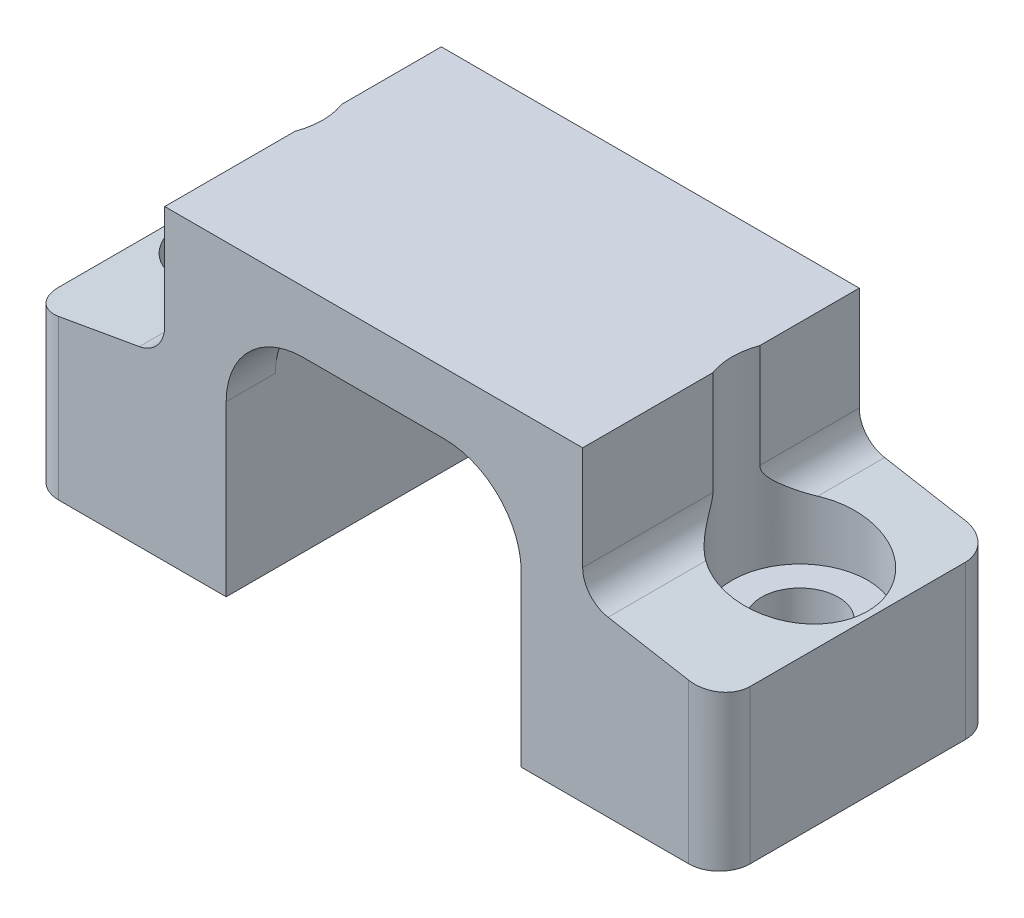
SolidWorks part; units mm, degrees
ref_plane "Front Plane" through (0, 0, 0) normal (0, 0, 1) x (1, 0, 0)
ref_plane "Top Plane" through (0, 0, 0) normal (0, 1, 0) x (1, 0, 0)
ref_plane "Right Plane" through (0, 0, 0) normal (1, 0, 0) x (0, 0, -1)
sketch "Sketch1" plane through (0, 0, 0) normal (0, 0, 1) x (1, 0, 0)
  line L0 (-92.6582, 0) -> (89.2369, 0) construction
  line L2 (-6.096, 10.16) -> (6.096, 10.16)
  line L3 (6.096, 10.16) -> (6.096, 0)
  line L4 (-6.096, 0) -> (6.096, 0) construction
  line L5 (8.89, 6.35) -> (14.2875, 6.35) construction
  line L6 (14.2875, 6.35) -> (14.2875, 0)
  line L7 (14.2875, 0) -> (6.096, 0)
  line L8 (8.636, 7.3465) -> (8.636, 12.7)
  line L9 (8.636, 12.7) -> (-8.636, 12.7)
  line L10 (0, 0) -> (0, 31.7739) construction
  line L13 (-8.636, 7.3465) -> (-8.636, 12.7)
  line L14 (-8.89, 6.35) -> (-14.2875, 6.35) construction
  line L15 (-14.2875, 6.35) -> (-14.2875, 0)
  line L16 (-14.2875, 0) -> (-6.096, 0)
  line L17 (-6.096, 10.16) -> (-6.096, 0)
  line L18 (14.2875, 6.35) -> (8.636, 7.3465)
  line L19 (-14.2875, 6.35) -> (-8.636, 7.3465)
  point P5 (0, 0)
  point P16 (0, 12.7)
  point P24 (0, 10.16)
  dimension "D1" = 10.16
  dimension "D2" = 2.54
  dimension "D3" = 12.192
  dimension "D4" = 12.7
  dimension "D5" = 6.35
  dimension "D7" = 28.575
  dimension "D8" = 10
  dimension "D9" = 10
extrude "Boss-Extrude1" add sketch "Sketch1" against normal blind 22.86
sketch "Sketch2" plane through (0, 0, 0) normal (0, 0, 1) x (1, 0, 0)
  line L0 (6.096, 10.16) -> (6.096, 0) construction
  line L1 (-6.096, 10.16) -> (6.096, 10.16) construction
  line L2 (6.096, 6.985) -> (6.096, 0) construction
  line L3 (-6.096, 10.16) -> (2.921, 10.16) construction
  line L4 (2.921, 10.16) -> (6.096, 10.16)
  line L5 (6.096, 10.16) -> (6.096, 6.985)
  line L6 (0, 0) -> (0, 17.4905) construction
  line L7 (-6.096, 10.16) -> (-6.096, 6.985)
  line L8 (-2.921, 10.16) -> (-6.096, 10.16)
  arc A0 (6.096, 6.985) -> (2.921, 10.16) centre (2.921, 6.985) ccw
  arc A1 (-6.096, 6.985) -> (-2.921, 10.16) centre (-2.921, 6.985) cw
  dimension "D1" = 3.175
extrude "Boss-Extrude2" add sketch "Sketch2" against normal blind 13.462
sketch "Sketch3" plane through (0, 0, -13.462) normal (0, 0, 1) x (1, 0, 0)
  line L2 (-6.096, 10.16) -> (-6.096, 6.985)
  line L3 (-2.921, 10.16) -> (-6.096, 10.16)
  line L4 (-6.096, 10.16) -> (-6.096, 6.985)
  line L5 (-2.921, 10.16) -> (-6.096, 10.16)
  line L6 (6.096, 10.16) -> (2.921, 10.16)
  line L7 (6.096, 6.985) -> (6.096, 10.16)
  line L8 (6.096, 10.16) -> (2.921, 10.16) construction
  line L9 (6.096, 6.985) -> (6.096, 10.16) construction
  arc A1 (-2.921, 10.16) -> (-6.096, 6.985) centre (-2.921, 6.985) ccw
  arc A2 (-2.921, 10.16) -> (-6.096, 6.985) centre (-2.921, 6.985) ccw
  arc A3 (6.096, 6.985) -> (2.921, 10.16) centre (2.921, 6.985) ccw
  arc A4 (6.096, 6.985) -> (2.921, 10.16) centre (2.921, 6.985) ccw construction
  dimension "D1" = 0
  dimension "D2" = 0
extrude "Boss-Extrude3" add sketch "Sketch3" against normal blind 1.905 from offset 1.27 offset against normal yes
sketch "Sketch4" plane through (0, 0, -16.637) normal (0, 0, 1) x (1, 0, 0)
  line L2 (-6.096, 10.16) -> (-6.096, 6.985)
  line L3 (-2.921, 10.16) -> (-6.096, 10.16)
  line L4 (-6.096, 10.16) -> (-6.096, 6.985)
  line L5 (-2.921, 10.16) -> (-6.096, 10.16)
  arc A1 (-2.921, 10.16) -> (-6.096, 6.985) centre (-2.921, 6.985) ccw
  arc A2 (-2.921, 10.16) -> (-6.096, 6.985) centre (-2.921, 6.985) ccw
  dimension "D1" = 0
extrude "Boss-Extrude4" add sketch "Sketch4" against normal blind 3.81 from offset 1.27 offset against normal yes
sketch "Sketch5" plane through (0, 0, 0) normal (0, 1, 0) x (1, 0, 0)
  line L0 (-5.9055, 22.0472) -> (5.9055, 22.0472)
  line L1 (5.9055, 22.0472) -> (5.9055, 22.86)
  line L2 (5.9055, 22.86) -> (-5.9055, 22.86)
  line L3 (-5.9055, 22.86) -> (-5.9055, 22.0472)
  line L5 (-5.9055, 17.018) -> (5.9055, 17.018)
  line L6 (-5.9055, 17.018) -> (-5.9055, 17.8308)
  line L7 (-5.9055, 17.8308) -> (5.9055, 17.8308)
  line L8 (5.9055, 17.018) -> (5.9055, 17.8308)
  line L9 (-5.9055, 13.8176) -> (5.9055, 13.8176)
  line L10 (-5.9055, 13.8176) -> (-5.9055, 14.6304)
  line L11 (-5.9055, 14.6304) -> (5.9055, 14.6304)
  line L12 (5.9055, 13.8176) -> (5.9055, 14.6304)
  line L13 (-5.9055, 13.8176) -> (5.9055, 13.8176)
  line L14 (-5.9055, 13.8176) -> (-5.9055, -1.27)
  line L15 (-5.9055, -1.27) -> (5.9055, -1.27)
  line L16 (5.9055, 13.8176) -> (5.9055, -1.27)
  line L17 (-6.096, 22.86) -> (6.096, 22.86) construction
  point P12 (0, 22.0472)
  dimension "D1" = 0.8128
  dimension "D2" = 11.811
  dimension "D3" = 5.842
  dimension "D4" = 4.0132
  dimension "D5" = 24.13
ref_plane "Plane1" through (0, 0, -5.08) normal (0, 0, 1) x (1, 0, 0)
sketch "Sketch6" plane through (0, 0, -5.08) normal (0, 0, 1) x (1, 0, 0)
  line L0 (13.889, 6.4203) -> (8.636, 7.3465) construction
  line L1 (8.636, 7.3465) -> (9.0771, 9.8479) construction
  line L2 (9.0771, 9.8479) -> (14.33, 8.9217) construction
  line L3 (14.33, 8.9217) -> (13.889, 6.4203) construction
  line L4 (11.2625, 6.8834) -> (11.2625, -1.27) construction
  line L5 (6.096, 0) -> (14.2875, 0) construction
  line L6 (8.636, 7.3465) -> (8.636, 12.7) construction
  line L8 (11.2625, -1.27) -> (12.85, -1.27)
  line L9 (12.85, -1.27) -> (12.85, 6.6035)
  line L10 (12.85, 6.6035) -> (11.2625, 6.8834) construction
  line L11 (11.2625, 6.8834) -> (11.2625, -1.27)
  line L12 (11.2625, -1.27) -> (11.2625, -5.0048) construction
  line L13 (8.636, 7.3465) -> (8.636, 6.35) construction
  line L14 (8.636, 6.35) -> (14.2875, 6.35) construction
  line L15 (14.2875, 6.35) -> (8.636, 7.3465) construction
  line L16 (12.85, 9.4234) -> (12.85, 6.6035)
  line L17 (11.2625, 6.8834) -> (11.2625, 9.4234)
  line L18 (11.2625, 9.4234) -> (12.85, 9.4234)
  dimension "D1" = 5.334
  dimension "D2" = 10
  dimension "D3" = 2.54
  dimension "D4" = 3.175
  dimension "D5" = 1.27
  dimension "D6" = 2.54
revolve "Cut-Revolve1" cut sketch "Sketch6" angle 360 about L12
mirror "Mirror1" about plane through (0, 0, 0) normal (1, 0, 0) of "Cut-Revolve1"
ref_plane "Plane2" through (0, 0, -11.43) normal (0, 0, 1) x (1, 0, 0)
mirror "Mirror2" about plane through (0, 0, -11.43) normal (0, 0, 1) of "Mirror1", "Cut-Revolve1"
sketch "Sketch8" plane through (0, 12.7, 0) normal (0, -1, 0) x (-1, 0, 0)
  circle A0 centre (11.2625, 5.08) radius 1.5875
  circle A1 centre (-11.2625, 5.08) radius 1.5875
  circle A2 centre (-11.2625, 17.78) radius 1.5875
  circle A3 centre (11.2625, 17.78) radius 1.5875
  circle A4 centre (11.2625, 17.78) radius 2.8
  circle A5 centre (11.2625, 5.08) radius 2.8
  circle A6 centre (-11.2625, 5.08) radius 2.8
  circle A7 centre (-11.2625, 17.78) radius 2.8
  dimension "D1" = 5.6
extrude "Cut-Extrude1" cut sketch "Sketch8" along normal blind 8
sketch "Sketch9" plane through (0, 0, 0) normal (0, -1, 0) x (-1, 0, 0)
  line L0 (14.2875, 22.86) -> (14.2875, 0) construction
  line L1 (-14.2875, 0) -> (14.2875, 0)
  line L2 (-14.2875, 0) -> (-14.2875, 11.43)
  line L3 (-14.2875, 11.43) -> (14.2875, 11.43)
  line L4 (14.2875, 0) -> (14.2875, 11.43)
  line L5 (-14.2875, 0) -> (14.2875, 11.43) construction
  line L6 (-14.2875, 11.43) -> (14.2875, 0) construction
  point P4 (0, 5.715)
extrude "Cut-Extrude2" cut sketch "Sketch9" against normal through all
fillet "Fillet1" radius 1.27 8 edges at (-14.2875, 3.175, -22.86) (14.2875, 3.175, -22.86) (-8.636, 7.3465, -14.1198) (-8.636, 7.3465, -20.8052) (8.636, 7.3465, -20.8052) (8.636, 7.3465, -14.1198) (14.2875, 3.175, -11.43) (-14.2875, 3.175, -11.43)
